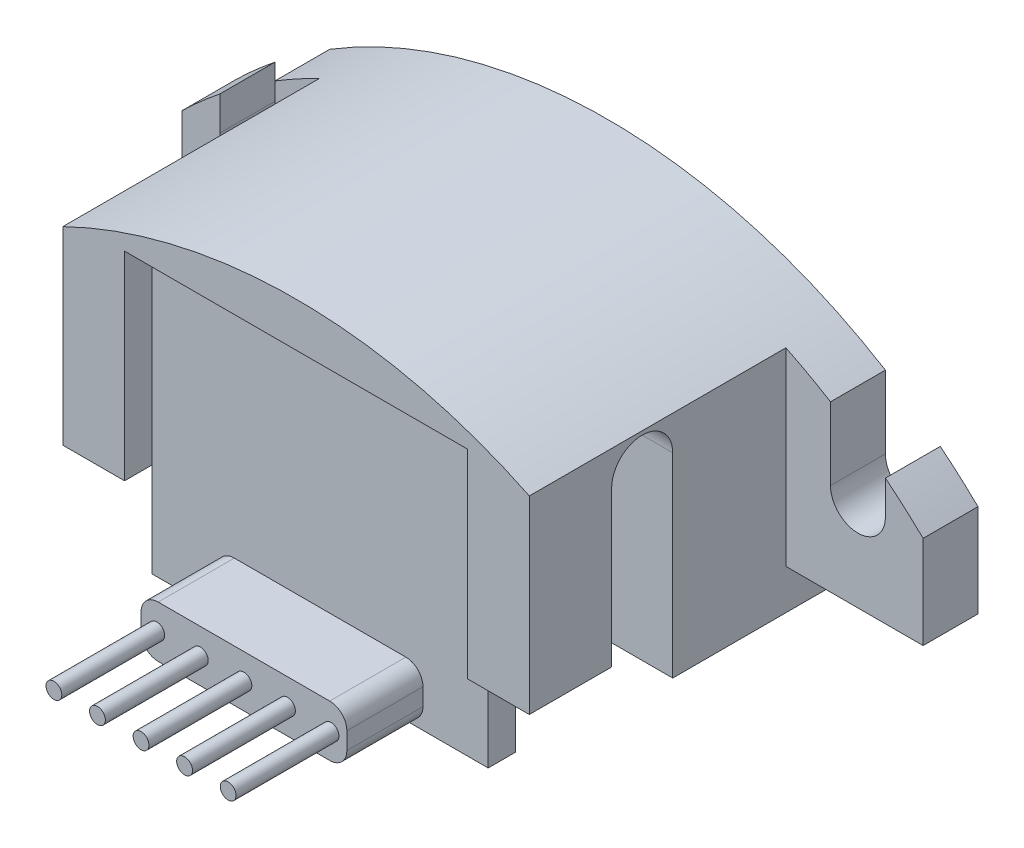
SolidWorks part; units mm, degrees
ref_plane "Plan de face" through (0, 0, 0) normal (0, 0, 1) x (1, 0, 0)
ref_plane "Plan de dessus" through (0, 0, 0) normal (0, 1, 0) x (1, 0, 0)
ref_plane "Plan de droite" through (0, 0, 0) normal (1, 0, 0) x (0, 0, -1)
sketch "Esquisse1" plane through (0, 0, 0) normal (0, 0, 1) x (1, 0, 0)
  line L0 (-8.9, 0) -> (8.9, 0) construction
  line L1 (-10.8, 0.018) -> (-10.8, -2.69)
  line L2 (-10.8, -2.69) -> (10.8, -2.69)
  line L3 (10.8, -2.69) -> (10.8, 0.018)
  line L4 (-9.7, 0) -> (-9.7, 0.9897)
  line L5 (-8.1, 0) -> (-8.1, 2.1151)
  line L6 (8.1, 0) -> (8.1, 2.1151)
  line L7 (9.7, 0) -> (9.7, 0.9897)
  arc A0 (10.8, 0.018) -> (9.7, 0.9897) centre (0, -11.1) ccw
  arc A1 (-9.7, 0) -> (-8.1, 0) centre (-8.9, 0) ccw
  arc A2 (8.1, 0) -> (9.7, 0) centre (8.9, 0) ccw
  arc A3 (-9.7, 0.9897) -> (-10.8, 0.018) centre (0, -11.1) ccw
  arc A4 (8.1, 2.1151) -> (-8.1, 2.1151) centre (0, -11.1) ccw
  point P3 (0, 0)
  point P5 (0, 4.4)
  dimension "D2" = 31
  dimension "D3" = 1.6
  dimension "D1" = 17.8
  dimension "D4" = 4.4
  dimension "D5" = 21.6
  dimension "D6" = 2.69
extrude "Boss.-Extru.1" add sketch "Esquisse1" along normal blind 1.6
sketch "Esquisse2" plane through (0, 0, 1.6) normal (0, 0, 1) x (1, 0, 0)
  line L0 (-10.8, -2.69) -> (10.8, -2.69) construction
  line L2 (-6.8, 2.8287) -> (-6.8, -2.69)
  line L3 (-6.8, -2.69) -> (6.8, -2.69)
  line L4 (6.8, 2.8287) -> (6.8, -2.69)
  arc A0 (8.1, 2.1151) -> (-8.1, 2.1151) centre (0, -11.1) ccw construction
  arc A1 (6.8, 2.8287) -> (-6.8, 2.8287) centre (0, -11.1) ccw
  dimension "D1" = 13.6
extrude "Boss.-Extru.2" add sketch "Esquisse2" along normal blind 7.48
sketch "Esquisse3" plane through (0, 0, 9.08) normal (0, 0, 1) x (1, 0, 0)
  line L0 (-6.8, -2.69) -> (6.8, -2.69) construction
  line L1 (-5, 3.11) -> (5, 3.11)
  line L2 (-5, 3.11) -> (-5, -2.69)
  line L3 (-5, -2.69) -> (5, -2.69)
  line L4 (5, 3.11) -> (5, -2.69)
  point P10 (0, 3.11)
  dimension "D1" = 10
  dimension "D2" = 5.8
extrude "Enlèv. mat.-Extru.2" cut sketch "Esquisse3" against normal blind 1.5
sketch "Esquisse4" plane through (-6.8, 0, 0) normal (-1, 0, 0) x (0, 0, 1)
  line L0 (5.79, -2.69) -> (5.79, 1.8287) construction
  line L1 (9.08, -2.69) -> (1.6, -2.69) construction
  line L2 (4.9, -2.69) -> (4.9, 1.8287)
  line L3 (6.68, -2.69) -> (6.68, 1.8287)
  line L6 (9.08, 2.8287) -> (9.08, -2.69) construction
  line L7 (9.08, 2.8287) -> (1.6, 2.8287) construction
  arc A0 (4.9, -2.69) -> (6.68, -2.69) centre (5.79, -2.69) ccw
  arc A1 (6.68, 1.8287) -> (4.9, 1.8287) centre (5.79, 1.8287) ccw
  point P4 (5.79, -0.4306)
  dimension "D1" = 0.89
  dimension "D2" = 1
  dimension "D3" = 2.4
extrude "Enlèv. mat.-Extru.3" cut sketch "Esquisse4" against normal through all
sketch "Esquisse5" plane through (0, 0, 0) normal (0, 0, -1) x (-1, 0, 0)
  line L0 (6.3, 0) -> (-6.3, 0) construction
  circle A0 centre (6.3, 0) radius 1
  circle A1 centre (-6.3, 0) radius 1
  point P3 (0, 0)
  dimension "D2" = 2
  dimension "D1" = 12.6
extrude "Boss.-Extru.3" add sketch "Esquisse5" along normal blind 0.8
ref_plane "Plan1" through (0, -0.8, 0) normal (0, 1, 0) x (1, 0, 0)
ref_plane "Plan2" through (0, -4.49, 0) normal (0, 1, 0) x (1, 0, 0)
sketch "Esquisse8" plane through (0, -4.49, 0) normal (0, 1, 0) x (1, 0, 0)
  line L0 (0, -7.58) -> (0, -9.5554) construction
  line L3 (0.23, -6.68) -> (0, -6.68)
  line L4 (0.23, -6.68) -> (0.23, -13.6)
  line L5 (0.23, -13.6) -> (0, -13.6)
  line L6 (0, -6.68) -> (0, -13.6)
  line L7 (-10.8, 0) -> (10.8, 0) construction
  line L9 (-6.8, -9.08) -> (-5, -9.08) construction
  dimension "D1" = 0.46
  dimension "D2" = 13.6
  dimension "D3" = 2.4
revolve "Révolution1" add sketch "Esquisse8" angle 360 about L0
pattern_linear "Répétition linéaire1" count 3 spacing 1.27 along (1, 0, 0) count 3 spacing 1.27 along (-1, 0, 0) of bodies 106
sketch "Esquisse10" plane through (0, 0, 7.58) normal (0, 0, 1) x (1, 0, 0)
  line L4 (-4.9, -2.59) -> (-4.9, -5.34)
  line L5 (-4.9, -5.34) -> (4.9, -5.34)
  line L6 (4.9, -5.34) -> (4.9, -2.59)
  line L8 (-4.9, 3.01) -> (-4.9, -2.59)
  line L9 (-4.9, -2.59) -> (4.9, -2.59)
  line L10 (4.9, -2.59) -> (4.9, 3.01)
  line L11 (4.9, 3.01) -> (-4.9, 3.01)
  line L12 (-4.9, 3.01) -> (-4.9, -2.59)
  line L14 (4.9, -2.59) -> (4.9, 3.01)
  line L15 (4.9, 3.01) -> (-4.9, 3.01)
  dimension "D2" = 5.34
  dimension "D1" = 0.1
extrude "Boss.-Extru.4" add sketch "Esquisse10" along normal blind 0.8
sketch "Esquisse11" plane through (0, 0, 0) normal (0, 0, -1) x (-1, 0, 0)
  line L0 (10.8, -2.69) -> (-10.8, -2.69) construction
  line L1 (6.8, -2.69) -> (-6.8, -2.69)
  line L2 (6.8, -2.69) -> (6.8, -3.86)
  line L3 (6.8, -3.86) -> (-6.8, -3.86)
  line L4 (-6.8, -2.69) -> (-6.8, -3.86)
  point P6 (0, -2.69)
  dimension "D1" = 13.6
  dimension "D2" = 1.17
extrude "Boss.-Extru.5" add sketch "Esquisse11" against normal up to surface (4.9 mm away) up to face at (0, -0.4306, 4.9)
sketch "Esquisse12" plane through (0, 0, 8.38) normal (0, 0, 1) x (1, 0, 0)
  line L1 (2.5, -5.24) -> (-2.5, -5.24)
  line L2 (3, -4.74) -> (3, -4.24)
  line L3 (2.5, -3.74) -> (-2.5, -3.74)
  line L4 (-3, -4.74) -> (-3, -4.24)
  line L5 (7.7952, -4.49) -> (-7.7952, -4.49) construction
  line L6 (-4.9, -5.34) -> (4.9, -5.34) construction
  arc A3 (-2.5, -5.24) -> (-3, -4.74) centre (-2.5, -4.74) cw
  arc A4 (-2.5, -3.74) -> (-3, -4.24) centre (-2.5, -4.24) ccw
  arc A5 (2.5, -5.24) -> (3, -4.74) centre (2.5, -4.74) ccw
  arc A6 (3, -4.24) -> (2.5, -3.74) centre (2.5, -4.24) ccw
  point P8 (3, -4.49)
  point P9 (0, -3.74)
  point P12 (0, -4.49)
  point P13 (-3, -5.24)
  point P19 (3, -5.24)
  dimension "D2" = 0.5
  dimension "D1" = 6
  dimension "D3" = 0.1
extrude "Boss.-Extru.6" add sketch "Esquisse12" along normal blind 2.22
sketch "Esquisse13" [suppressed] plane through (0, 0, 8.38) normal (0, 0, 1) x (1, 0, 0)
  line L4 (-2.5, -5.24) -> (2.5, -5.24)
  line L5 (3, -4.74) -> (3, -4.24)
  line L6 (2.5, -3.74) -> (-2.5, -3.74)
  line L7 (-3, -4.24) -> (-3, -4.74)
  line L8 (-2.5, -5.24) -> (2.5, -5.24)
  line L9 (3, -4.74) -> (3, -4.24)
  line L10 (2.5, -3.74) -> (-2.5, -3.74)
  line L11 (-3, -4.24) -> (-3, -4.74)
  arc A4 (-3, -4.74) -> (-2.5, -5.24) centre (-2.5, -4.74) ccw
  arc A5 (2.5, -5.24) -> (3, -4.74) centre (2.5, -4.74) ccw
  arc A6 (3, -4.24) -> (2.5, -3.74) centre (2.5, -4.24) ccw
  arc A7 (-2.5, -3.74) -> (-3, -4.24) centre (-2.5, -4.24) ccw
  arc A8 (-3, -4.74) -> (-2.5, -5.24) centre (-2.5, -4.74) ccw
  arc A9 (2.5, -5.24) -> (3, -4.74) centre (2.5, -4.74) ccw
  arc A10 (3, -4.24) -> (2.5, -3.74) centre (2.5, -4.24) ccw
  arc A11 (-2.5, -3.74) -> (-3, -4.24) centre (-2.5, -4.24) ccw
  dimension "D1" = 0
extrude "Enlèv. mat.-Extru.4" [suppressed] cut sketch "Esquisse13" along normal through all
sketch "Esquisse14" [suppressed] plane through (0, 0, 8.38) normal (0, 0, 1) x (1, 0, 0)
  line L5 (0, -10.7582) -> (0, 5.9488) construction
  line L7 (0, -10.34) -> (-0.375, -10.34)
  line L8 (0, -10.34) -> (0, -3.34)
  line L9 (0, -3.34) -> (-0.23, -3.34)
  line L10 (-0.23, -6.34) -> (-0.23, -3.34)
  line L11 (-4.9, -5.34) -> (4.9, -5.34) construction
  line L12 (-0.23, -6.34) -> (-0.375, -6.34)
  line L13 (-0.375, -6.34) -> (-0.375, -10.34)
  dimension "D1" = 0.46
  dimension "D2" = 5
  dimension "D3" = 2
  dimension "D4" = 0.75
  dimension "D5" = 1
revolve "Révolution2" [suppressed] add sketch "Esquisse14" angle 360 about L5
pattern_linear "Répétition linéaire2" [suppressed] count 3 spacing 1.27 count 3 spacing 1.28
